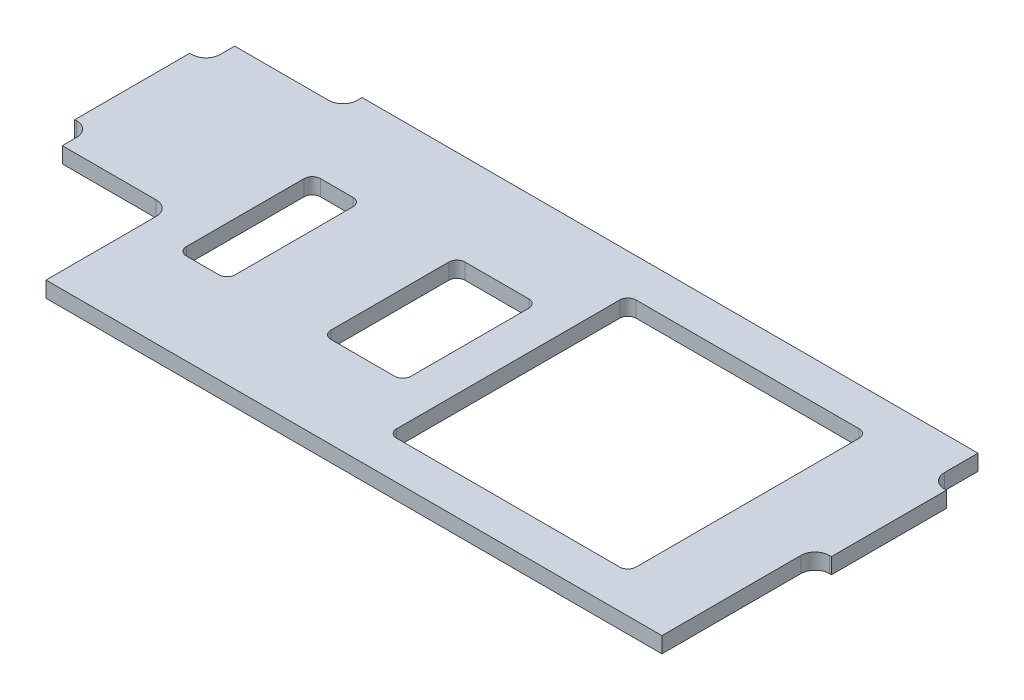
SolidWorks part; units mm, degrees
material "PVC hart"
ref_plane "Ebene vorne" through (0, 0, 0) normal (0, 0, 1) x (1, 0, 0)
ref_plane "Ebene oben" through (0, 0, 0) normal (0, 1, 0) x (1, 0, 0)
ref_plane "Ebene rechts" through (0, 0, 0) normal (1, 0, 0) x (0, 0, -1)
sketch "Skizze1" plane through (0, 0, 0) normal (0, 1, 0) x (1, 0, 0)
  line L0 (37.8, 16.5) -> (-26.5, 16.5)
  line L1 (37.8, -16.5) -> (-26.5, -16.5)
  line L2 (0, 16.5) -> (0, -16.5) construction
  line L3 (-17.1, 0) -> (0, 0) construction
  line L4 (0, 0) -> (5.25, 0) construction
  line L5 (5.25, 12.5) -> (30.25, 12.5)
  line L6 (-26.5, 14.5) -> (-37.8, 14.5)
  line L7 (5.25, 12.5) -> (5.25, -12.5)
  line L8 (5.25, -12.5) -> (30.25, -12.5)
  line L9 (30.25, 12.5) -> (30.25, -12.5)
  line L11 (-37.8, 14.5) -> (-37.8, 11.5)
  line L12 (-37.8, 11.5) -> (-39.5, 11.5)
  line L13 (-39.5, 11.5) -> (-39.5, -0.5)
  line L14 (-7.1, 7) -> (1.25, 7)
  line L15 (-7.1, 7) -> (-7.1, -7)
  line L16 (-7.1, -7) -> (1.25, -7)
  line L17 (1.25, 7) -> (1.25, -7)
  line L18 (-39.5, -0.5) -> (-37.8, -0.5)
  line L19 (-17.1, -7) -> (-17.1, 7)
  line L20 (-22.2, 7) -> (-17.1, 7)
  line L21 (-22.2, -7) -> (-22.2, 7)
  line L22 (-22.2, -7) -> (-17.1, -7)
  line L23 (-37.8, -0.5) -> (-37.8, -3.5)
  line L24 (-37.8, -3.5) -> (-26.5, -3.5)
  line L27 (39.5, -0.5) -> (37.8, -0.5)
  line L28 (37.8, -0.5) -> (37.8, -16.5)
  line L29 (-26.5, -16.5) -> (-26.5, 16.5)
  line L31 (39.5, 11.5) -> (39.5, -0.5)
  line L32 (37.8, 11.5) -> (39.5, 11.5)
  line L33 (37.8, 16.5) -> (37.8, 11.5)
  point P28 (-39.5, 5.5)
  dimension "D2" = 33
  dimension "D3" = 14
  dimension "D4" = 26.5
  dimension "D5" = 79
  dimension "D6" = 5.1
  dimension "D7" = 4.3
  dimension "D8" = 1.7
  dimension "D9" = 12
  dimension "D10" = 25
  dimension "D11" = 18
  dimension "D12" = 10
  dimension "D13" = 22
  dimension "D14" = 8.35
  dimension "D15" = 4
extrude "Aufsatz-Linear austragen1" add sketch "Skizze1" against normal mid plane 1.65
fillet "Verrundung1" radius 1.5 6 edges at (-26.5, 0, 3.5) (-26.5, 0, -14.5) (37.8, 0, -11.5) (37.8, 0, 0.5) (-37.8, 0, 0.5) (-37.8, 0, -11.5)
fillet "Verrundung2" radius 0.85 12 edges at (-22.2, 0, 7) (-17.1, 0, 7) (-17.1, 0, -7) (-22.2, 0, -7) (30.25, 0, -12.5) (30.25, 0, 12.5) (5.25, 0, 12.5) (5.25, 0, -12.5) (-7.1, 0, 7) (1.25, 0, 7) (1.25, 0, -7) (-7.1, 0, -7)
ref_plane "Ebene1" through (0, 0, -5.5) normal (0, 0, -1) x (-1, 0, 0)
